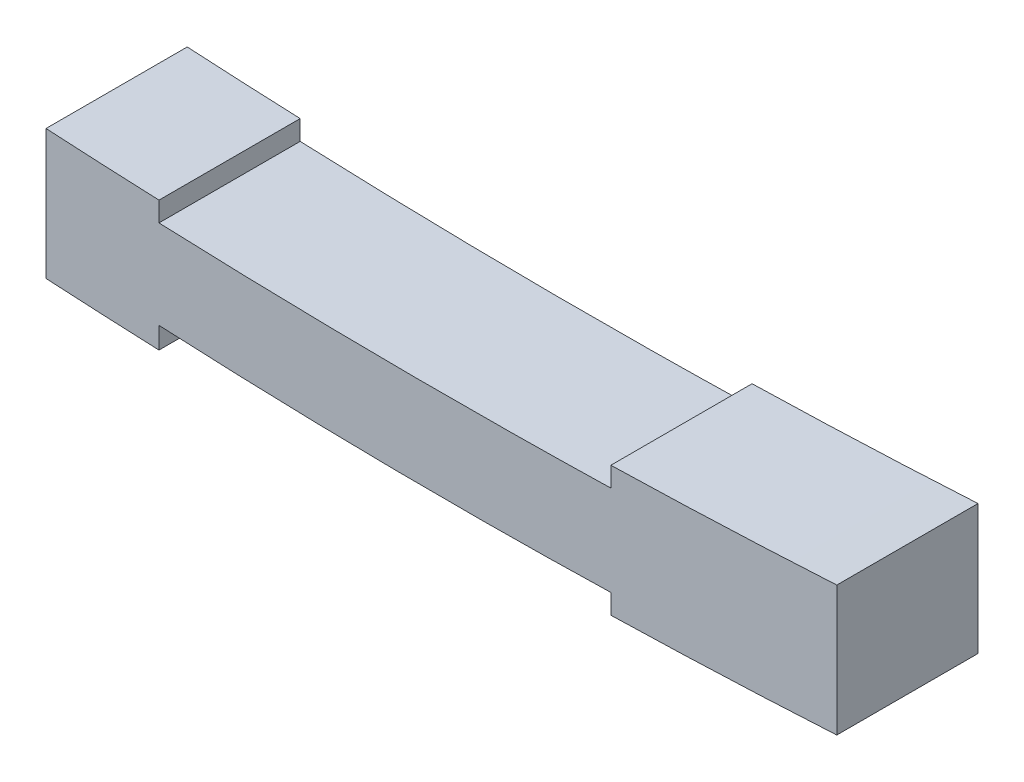
SolidWorks part; units mm, degrees
ref_plane "Front Plane" through (0, 0, 0) normal (0, 0, 1) x (1, 0, 0)
ref_plane "Top Plane" through (0, 0, 0) normal (0, 1, 0) x (1, 0, 0)
ref_plane "Right Plane" through (0, 0, 0) normal (1, 0, 0) x (0, 0, -1)
sketch "Sketch1" plane through (0, 0, 0) normal (0, 1, 0) x (1, 0, 0)
  line L1 (70, -12.5) -> (-70, -12.5)
  line L2 (70, -12.5) -> (70, 12.5)
  line L3 (70, 12.5) -> (-70, 12.5)
  line L4 (-70, -12.5) -> (-70, 12.5)
  line L5 (70, -12.5) -> (-70, 12.5) construction
  line L6 (70, 12.5) -> (-70, -12.5) construction
  point P0 (0, 0)
  point P5 (-70, 0)
  dimension "D1" = 140
  dimension "D2" = 25
extrude "Boss-Extrude1" add sketch "Sketch1" along normal blind 25
sketch "Sketch2" plane through (0, 0, 12.5) normal (0, 0, 1) x (1, 0, 0)
  line L0 (-70, 22.8376) -> (70, 22.8376)
  line L1 (-70, 25) -> (-70, 0) construction
  line L2 (70, 25) -> (70, 0) construction
  spline S0 degree 2 poles (-70, 12.5) (0, 10.0003) (70, 12.5) knots 0 0 0 1 1 1
  point P8 (-500000, 60752.5992)
sketch "Sketch3" plane through (-70, 0, 0) normal (-1, 0, 0) x (0, 0, 1)
  line L0 (12.5, 25) -> (-12.5, 0)
  line L1 (-12.5, 25) -> (12.5, 0)
  circle A0 centre (0, 12.5) radius 12.5
  point P10 (14.9425, 56.9827)
sketch "Sketch4" plane through (70, 0, 0) normal (1, 0, 0) x (0, 0, -1)
  line L0 (12.5, 25) -> (-12.5, 0)
  line L1 (-12.5, 25) -> (12.5, 0)
  circle A0 centre (0, 12.5) radius 12.4007
  point P10 (-7.4057, 0.9787)
sketch "Sketch5" plane through (0, 0, 12.5) normal (0, 0, 1) x (1, 0, 0)
  line L0 (30, 23.3673) -> (30, 19.8673)
  line L1 (-70, 25) -> (70, 25)
  line L2 (-50, 24.0204) -> (-50, 20.5204)
  line L3 (-70, 25) -> (70, 25) construction
  line L4 (-50, 20.5204) -> (-50, 1.0204)
  line L5 (30, 25) -> (-50, 25)
  line L6 (0, 11.2502) -> (0, 25)
  line L7 (-70, 21.5) -> (-50, 21.5)
  line L8 (0, 11.2502) -> (0, 14.7502)
  line L9 (-70, 25) -> (-70, 21.5)
  line L10 (-50, 1.0204) -> (-50, 4.813)
  line L11 (-70, 0) -> (-70, 2)
  line L12 (-70, 2) -> (-70, 0)
  line L13 (-70, 0) -> (70, 0)
  line L14 (70, 0) -> (70, 2)
  line L15 (0, 23) -> (0, 19.5)
  line L16 (30, 23.3673) -> (30, 0.3673)
  line L17 (30, 0.3673) -> (30, 3.8673)
  line L18 (0, 0) -> (0, 3.5)
  spline S0 degree 2 poles (-70, 25) (0, 21) (70, 25) knots 0 0 0 1 1 1
  spline S1 degree 2 poles (-70, 2) (0, -2) (70, 2) knots 0 0 0 1 1 1
  spline S2 degree 2 poles (-50, 20.5204) (-10.0053, 18.8878) (30, 19.8673) knots 0 0 0 1 1 1
  spline S3 degree 2 poles (-50, 4.813) (-10.0108, 2.8) (30, 3.8673) knots 0 0 0 1 1 1
  point P34 (0, 0)
  line M4 (-70, 0) -> (70, 0)
  line M5 (70, 0) -> (70, 25)
  line M6 (70, 25) -> (-70, 25)
  line M7 (-70, 25) -> (-70, 0)
  dimension "D1" = 3.5
  dimension "D2" = 3.5
  dimension "D3" = 3.5
  dimension "D4" = 3.5
  dimension "D5" = 3.5
  dimension "D6" = 3.5
  dimension "D7" = 3.5
  dimension "D8" = 3.5
extrude "Cut-Extrude1" cut sketch "Sketch5" against normal blind 25 contours S0 L6 L5 M6 | L6 S0 L1 M6 | L6 S2 L0 S0 | L2 S2 L6 S0 | S3 L4 S1 L18 | S3 L18 S1 L16 | S1 L13 M5 | S1 M7 M4
sketch "Sketch6" plane through (0, 0, 12.5) normal (0, 0, 1) x (1, 0, 0)
  line L0 (30, 19.8673) -> (30, 3.8673)
  line L1 (-50, 20.5204) -> (-50, 4.813)
  parabola Q0 (-50, 20.5204) -> (30, 19.8673) focus (-2.502, 632.0306) apex (-5.0014, 19.5102) construction
  parabola Q1 (-50, 4.813) -> (30, 3.8673) focus (-1.3639, 522.9715) apex (-5.0028, 3.523) construction
  spline S0 degree 2 poles (-50, 20.5204) (-10.0098, 18.8878) (30, 19.8673) knots 0 0 0 1 1 1
  spline S1 degree 2 poles (-50, 4.813) (-10.017, 2.8001) (30, 3.8673) knots 0 0 0 1 1 1
